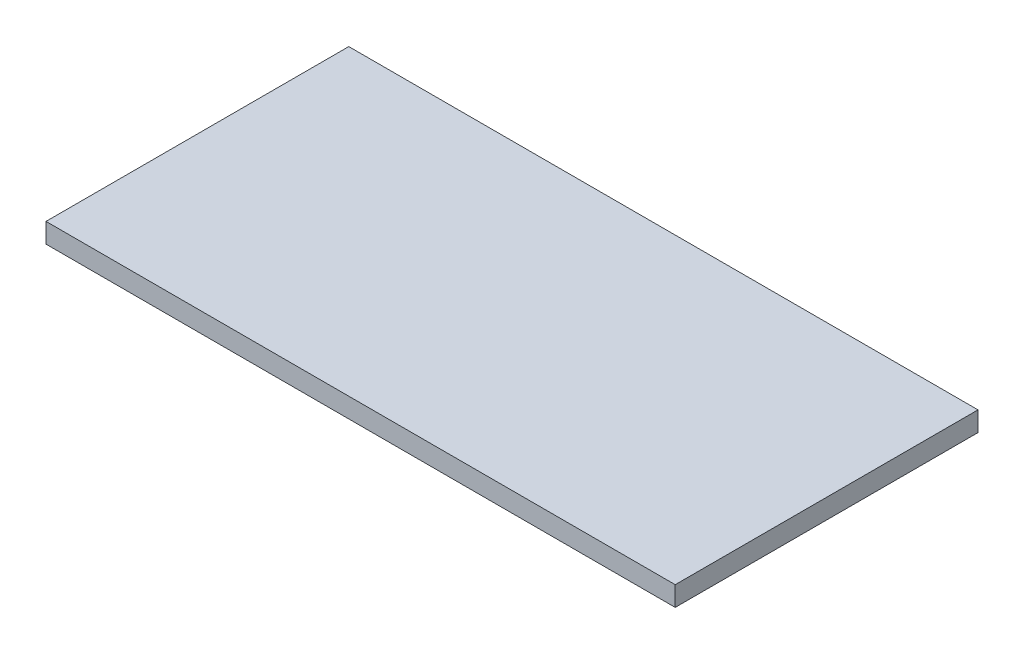
SolidWorks part; units mm, degrees
ref_plane "Front Plane" through (0, 0, 0) normal (0, 0, 1) x (1, 0, 0)
ref_plane "Top Plane" through (0, 0, 0) normal (0, 1, 0) x (1, 0, 0)
ref_plane "Right Plane" through (0, 0, 0) normal (1, 0, 0) x (0, 0, -1)
sketch "Sketch1" plane through (0, 0, 0) normal (0, 1, 0) x (1, 0, 0)
  line L1 (0, 0) -> (202.692, 0)
  line L2 (0, 0) -> (0, 97.536)
  line L3 (0, 97.536) -> (202.692, 97.536)
  line L4 (202.692, 0) -> (202.692, 97.536)
  dimension "D1" = 202.692
  dimension "D2" = 97.536
extrude "Boss-Extrude1" add sketch "Sketch1" along normal blind 6.35
